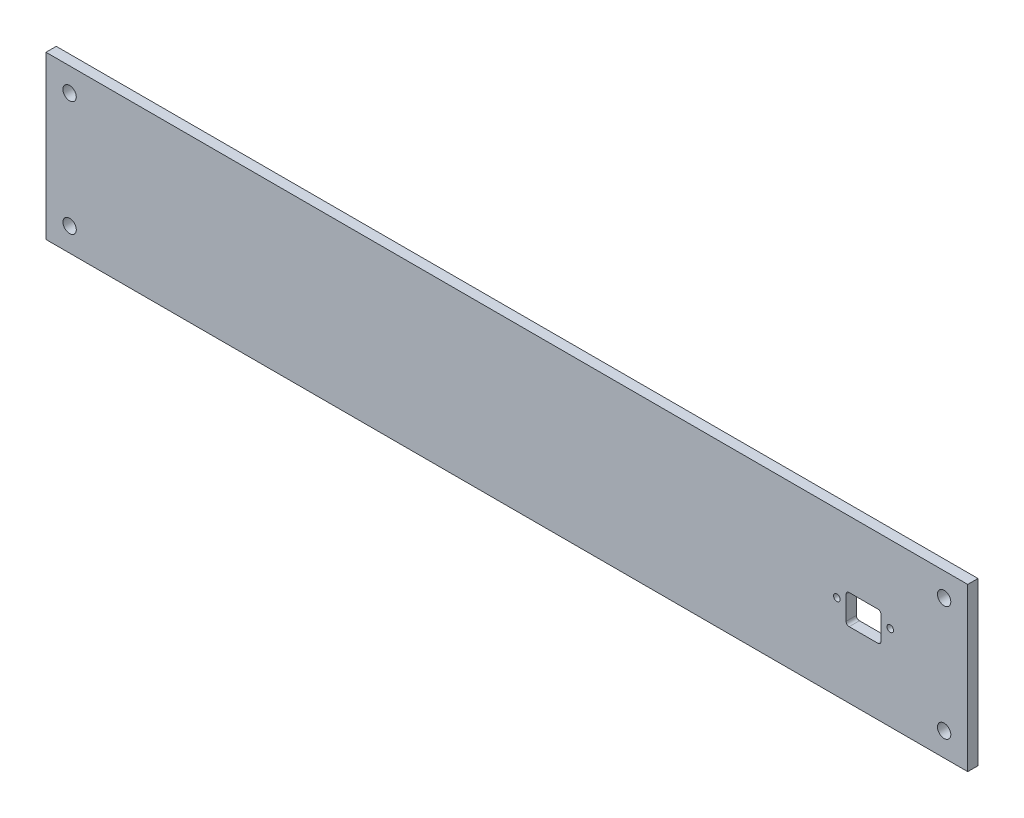
SolidWorks part; units mm, degrees
ref_plane "Piano frontale" through (0, 0, 0) normal (0, 0, 1) x (1, 0, 0)
ref_plane "Piano superiore" through (0, 0, 0) normal (0, 1, 0) x (1, 0, 0)
ref_plane "Piano destro" through (0, 0, 0) normal (1, 0, 0) x (0, 0, -1)
sketch "f" plane through (0, 0, 0) normal (0, 0, 1) x (1, 0, 0)
  line L0 (0, 0) -> (0, 79)
  line L1 (0, 79) -> (449, 79)
  line L2 (449, 79) -> (449, 0)
  line L3 (449, 0) -> (0, 0)
  line L4 (0, 39.5) -> (449, 39.5) construction
  line L5 (224.5, 42) -> (224.5, 123.488) construction
  line L6 (406.7469, 33.8) -> (406.7469, 45.2)
  line L7 (405.2469, 46.7) -> (391.2469, 46.7)
  line L8 (389.7469, 45.2) -> (389.7469, 33.8)
  line L9 (405.2469, 32.3) -> (391.2469, 32.3)
  line L10 (449, 79) -> (224.5, 0) construction
  line L11 (334, 39.5) -> (334, 81.5) construction
  line L12 (224.5, 0) -> (0, 79) construction
  line L13 (112.25, 42) -> (112.25, 84) construction
  line L14 (383.7289, 41.5) -> (410.6038, 41.5) construction
  line L15 (398.2469, 46.7) -> (398.2469, 32.3) construction
  circle A0 centre (11.5, 67.5) radius 3.25
  circle A1 centre (437.5, 67.5) radius 3.25
  circle A2 centre (11.5, 11.5) radius 3.25
  circle A3 centre (437.5, 11.5) radius 3.25
  circle A4 centre (385.2469, 41.5) radius 1.6
  circle A5 centre (411.2469, 41.5) radius 1.6
  arc A6 (406.7469, 45.2) -> (405.2469, 46.7) centre (405.2469, 45.2) ccw
  arc A7 (406.7469, 33.8) -> (405.2469, 32.3) centre (405.2469, 33.8) cw
  arc A8 (391.2469, 32.3) -> (389.7469, 33.8) centre (391.2469, 33.8) cw
  arc A9 (389.7469, 45.2) -> (391.2469, 46.7) centre (391.2469, 45.2) cw
  point P25 (406.7469, 39.5)
  point P26 (389.7469, 39.5)
  point P38 (406.7469, 46.7)
  point P41 (406.7469, 32.3)
  point P44 (389.7469, 32.3)
  point P47 (389.7469, 46.7)
  dimension "D3" = 11.5
  dimension "D4" = 11.5
  dimension "D6" = 17
  dimension "D9" = 2
  dimension "D10" = 1.5
  dimension "D5" = 6.5
  dimension "D8" = 3.2
  dimension "D1" = 79
  dimension "D2" = 449
  dimension "D7" = 7.2
  dimension "D11" = 13
extrude "Estrusione-Estrusione1" add sketch "f" along normal blind 5
